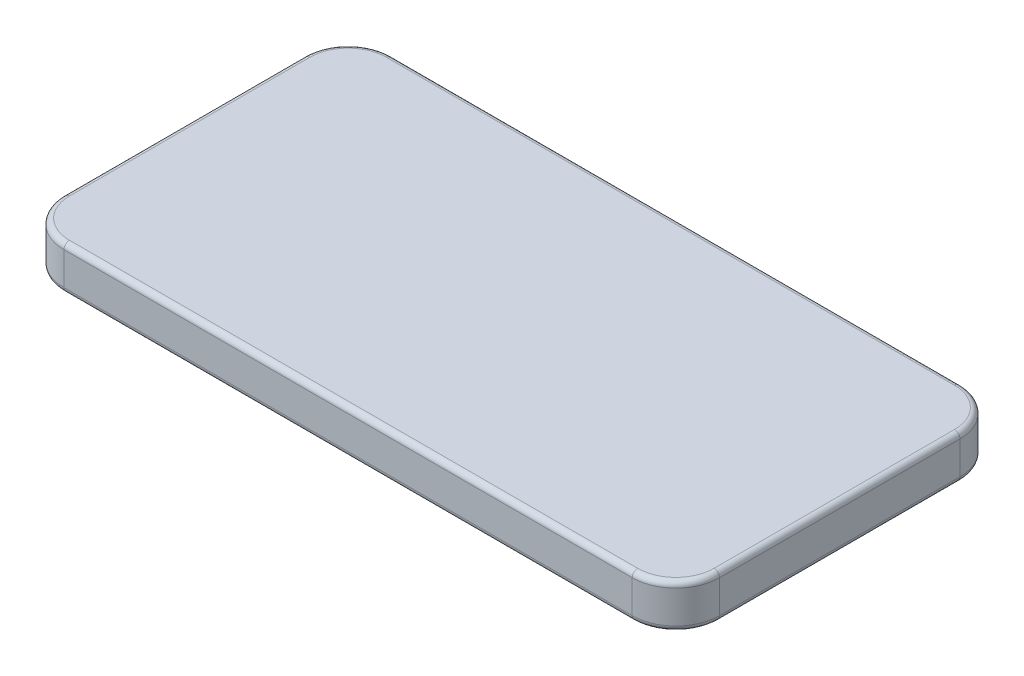
SolidWorks part; units mm, degrees
ref_plane "Front Plane" through (0, 0, 0) normal (0, 0, 1) x (1, 0, 0)
ref_plane "Top Plane" through (0, 0, 0) normal (0, 1, 0) x (1, 0, 0)
ref_plane "Right Plane" through (0, 0, 0) normal (1, 0, 0) x (0, 0, -1)
sketch "Sketch1" plane through (0, 0, 0) normal (0, 1, 0) x (1, 0, 0)
  line L1 (50.8, 0) -> (711.2, 0)
  line L2 (0, 50.8) -> (0, 330.2)
  line L3 (50.8, 381) -> (711.2, 381)
  line L4 (762, 50.8) -> (762, 330.2)
  arc A0 (0, 330.2) -> (50.8, 381) centre (50.8, 330.2) cw
  arc A1 (0, 50.8) -> (50.8, 0) centre (50.8, 50.8) ccw
  arc A2 (762, 50.8) -> (711.2, 0) centre (711.2, 50.8) cw
  arc A3 (762, 330.2) -> (711.2, 381) centre (711.2, 330.2) ccw
  point P7 (0, 381)
  point P10 (0, 0)
  point P15 (762, 381)
  dimension "D3" = 50.8
  dimension "D4" = 50.8
  dimension "D1" = 762
  dimension "D2" = 381
extrude "Boss-Extrude1" add sketch "Sketch1" along normal blind 50.8
fillet "Fillet1" radius 6.35 8 edges at (14.879, 50.8, -14.879) (0, 50.8, -190.5) (14.879, 50.8, -366.121) (381, 50.8, -381) (747.121, 50.8, -366.121) (762, 50.8, -190.5) (747.121, 50.8, -14.879) (381, 50.8, 0)
fillet "Fillet2" radius 6.35 8 edges at (14.879, 0, -366.121) (381, 0, -381) (747.121, 0, -366.121) (762, 0, -190.5) (747.121, 0, -14.879) (381, 0, 0) (14.879, 0, -14.879) (0, 0, -190.5)
